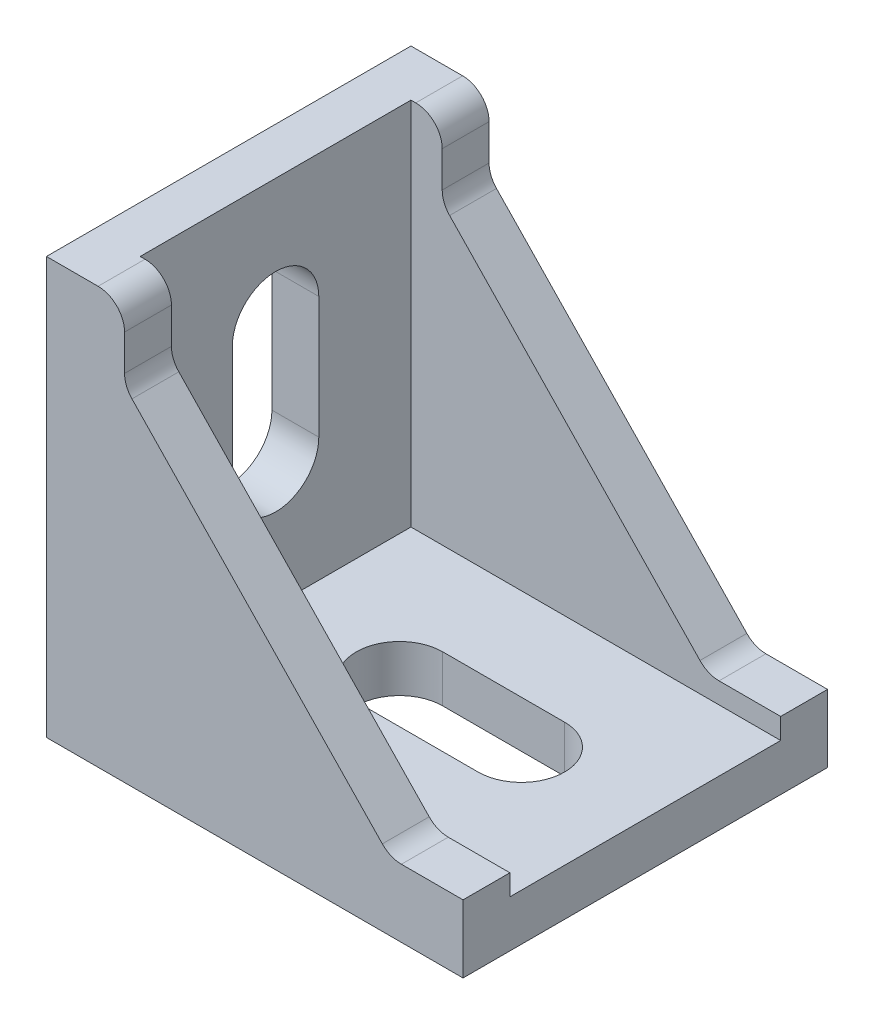
SolidWorks part; units mm, degrees
ref_plane "Front Plane" through (0, 0, 0) normal (0, 0, 1) x (1, 0, 0)
ref_plane "Top Plane" through (0, 0, 0) normal (0, 1, 0) x (1, 0, 0)
ref_plane "Right Plane" through (0, 0, 0) normal (1, 0, 0) x (0, 0, -1)
sketch "Sketch1" plane through (0, 0, 0) normal (0, 0, 1) x (1, 0, 0)
  line L0 (-20, 17.75) -> (-15.5, 17.75)
  line L3 (-20, -22.25) -> (20, -22.25)
  line L6 (-20, -22.25) -> (-20, 17.75)
  line L9 (-15.5, 17.75) -> (-15.5, -17.75)
  line L10 (-15.5, -17.75) -> (20, -17.75)
  line L11 (20, -17.75) -> (20, -22.25)
  point P3 (3.871, 10.3226)
  point P7 (0, -22.25)
  point P8 (-10.5376, 5.1613)
  point P10 (-15.5, -4.3011)
  point P11 (-15.5, 0)
  dimension "D1" = 40
  dimension "D2" = 40
  dimension "D3" = 4.5
  dimension "D4" = 4.5
extrude "Boss-Extrude1" add sketch "Sketch1" along normal mid plane 35
sketch "Sketch2" plane through (0, 0, 17.5) normal (0, 0, 1) x (1, 0, 0)
  line L0 (-15.5, 17.75) -> (-12.5, 17.75)
  line L1 (-12.5, 17.75) -> (-12.5, 10.75)
  line L2 (-12.5, 10.75) -> (13, -15.75)
  line L3 (13, -15.75) -> (20, -15.75)
  line L4 (20, -17.75) -> (-15.5, -17.75) construction
  line L7 (20, -15.75) -> (20, -17.75)
  line L8 (-15.5, 17.75) -> (-15.5, -17.75)
  line L9 (-15.5, -17.75) -> (20, -17.75)
  dimension "D1" = 3
  dimension "D2" = 7
  dimension "D3" = 7
  dimension "D4" = 2
extrude "Boss-Extrude2" add sketch "Sketch2" against normal blind 4.5
mirror "Mirror1" about plane through (0, 0, 0) normal (0, 0, 1) of "Boss-Extrude2"
sketch "Sketch3" plane through (-15.5, 0, 0) normal (1, 0, 0) x (0, 0, -1)
  line L0 (0, 5.85) -> (0, -5.85) construction
  line L1 (4.15, 5.85) -> (4.15, -5.85)
  line L2 (-4.15, 5.85) -> (-4.15, -5.85)
  line L3 (13, 17.75) -> (13, -17.75) construction
  arc A0 (4.15, 5.85) -> (-4.15, 5.85) centre (0, 5.85) ccw
  arc A1 (-4.15, -5.85) -> (4.15, -5.85) centre (0, -5.85) ccw
  point P3 (0, 0)
  point P8 (0, 0)
  point P9 (13, 0)
  point P14 (0, 10)
  point P15 (0, -10)
  dimension "D1" = 8.3
  dimension "D2" = 20
extrude "Cut-Extrude1" cut sketch "Sketch3" against normal through all
sketch "Sketch4" plane through (0, -17.75, 0) normal (0, 1, 0) x (1, 0, 0)
  line L0 (-3.6, 0) -> (8.1, 0) construction
  line L1 (-3.6, 4.15) -> (8.1, 4.15)
  line L2 (-3.6, -4.15) -> (8.1, -4.15)
  line L3 (-15.5, 13) -> (20, 13)
  arc A0 (-3.6, 4.15) -> (-3.6, -4.15) centre (-3.6, 0) ccw
  arc A1 (8.1, -4.15) -> (8.1, 4.15) centre (8.1, 0) ccw
  point P3 (2.25, 0)
  point P8 (-7.75, 0)
  point P9 (12.25, 0)
  point P10 (2.25, 13)
  dimension "D1" = 8.3
  dimension "D2" = 20
extrude "Cut-Extrude2" cut sketch "Sketch4" against normal through all
fillet "Fillet1" radius 2.54 6 edges at (13, -15.75, -15.25) (13, -15.75, 15.25) (-12.5, 10.75, 15.25) (-12.5, 10.75, -15.25) (-12.5, 17.75, -15.25) (-12.5, 17.75, 15.25)
equation "\"D4@Sketch1\"=\"D3@Sketch1\""
